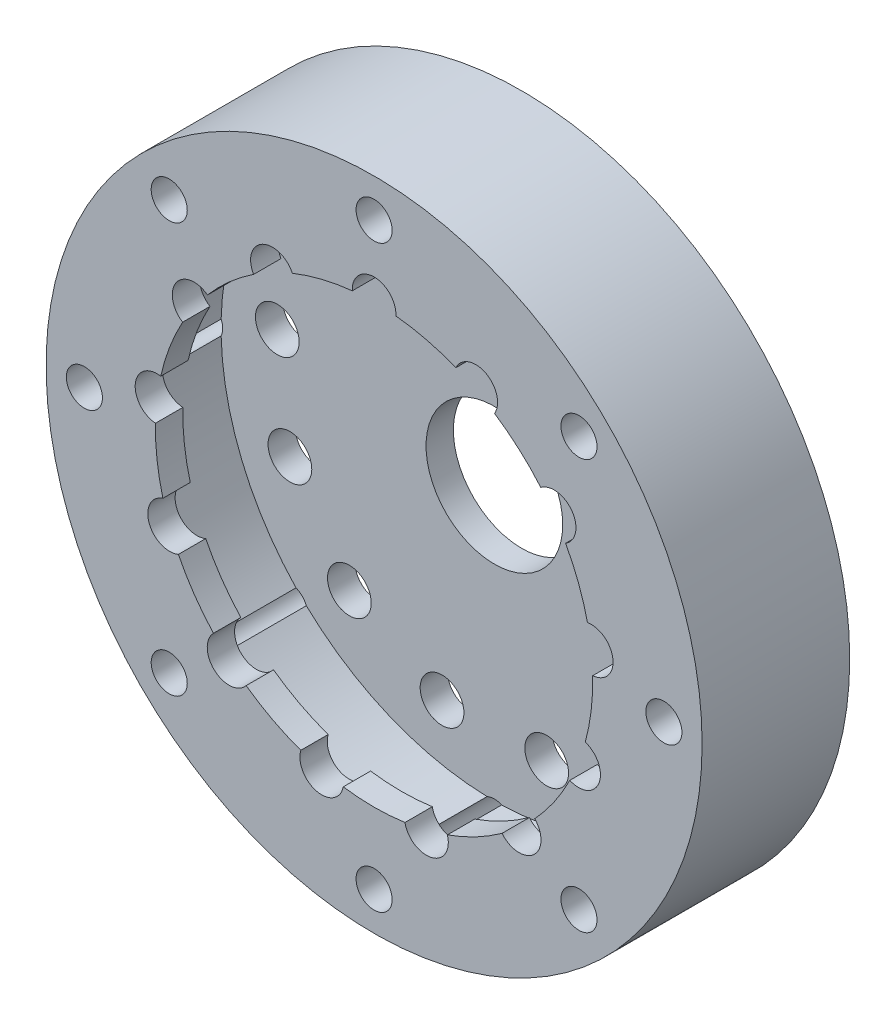
SolidWorks part; units mm, degrees
ref_plane "Front Plane" through (0, 0, 0) normal (0, 0, 1) x (1, 0, 0)
ref_plane "Top Plane" through (0, 0, 0) normal (0, 1, 0) x (1, 0, 0)
ref_plane "Right Plane" through (0, 0, 0) normal (1, 0, 0) x (0, 0, -1)
sketch "Sketch1" plane through (0, 0, 0) normal (0, 0, 1) x (1, 0, 0)
  circle A0 centre (0, 0) radius 60
  circle A1 centre (0, 0) radius 55 construction
  dimension "D1" = 120
  dimension "D2" = 5
extrude "Boss-Extrude1" add sketch "Sketch1" along normal blind 5
sketch "Sketch2" plane through (0, 0, 5) normal (0, 0, 1) x (1, 0, 0)
  circle A0 centre (0, 0) radius 60
  circle A1 centre (0, 0) radius 50
  circle A2 centre (0, 0) radius 60 construction
  dimension "D1" = 10
extrude "Boss-Extrude2" add sketch "Sketch2" along normal blind 22
sketch "Sketch3" plane through (0, 0, 27) normal (0, 0, 1) x (1, 0, 0)
  circle A0 centre (0, 0) radius 60
  circle A2 centre (0, 0) radius 60 construction
  circle A3 centre (0, 0) radius 40
  dimension "D1" = 80
extrude "Boss-Extrude3" add sketch "Sketch3" against normal blind 5
sketch "Sketch4" plane through (0, 0, 5) normal (0, 0, 1) x (1, 0, 0)
  circle A0 centre (0, 0) radius 12.5
  dimension "D1" = 25
extrude "Cut-Extrude1" cut sketch "Sketch4" against normal through all
sketch "Sketch5" plane through (0, 0, 27) normal (0, 0, 1) x (1, 0, 0)
  circle A14 centre (0, 40) radius 4
  circle A15 centre (0, 0) radius 40 construction
  circle A16 centre (18.5889, 35.4182) radius 4
  circle A17 centre (32.9194, 22.7226) radius 4
  circle A18 centre (39.7084, 4.8215) radius 4
  circle A19 centre (37.4006, -14.1842) radius 4
  circle A20 centre (26.5249, -29.9404) radius 4
  circle A21 centre (9.5726, -38.8377) radius 4
  circle A22 centre (-9.5726, -38.8377) radius 4
  circle A23 centre (-26.5249, -29.9404) radius 4
  circle A24 centre (-37.4006, -14.1842) radius 4
  circle A25 centre (-39.7084, 4.8215) radius 4
  circle A26 centre (-32.9194, 22.7226) radius 4
  circle A27 centre (-18.5889, 35.4182) radius 4
  point P30 (0, 0)
  dimension "D1" = 8
  dimension "D2" = 80
extrude "Cut-Extrude2" cut sketch "Sketch5" against normal through all
sketch "Sketch13" plane through (0, 0, 27) normal (0, 0, 1) x (1, 0, 0)
  circle A0 centre (0, 0) radius 53 construction
  circle A1 centre (0, 0) radius 60 construction
  point P5 (0, 53)
  point P6 (37.4767, 37.4767)
  point P9 (53, 0)
  point P10 (37.4767, -37.4767)
  point P11 (0, -53)
  point P12 (-37.4767, -37.4767)
  point P13 (-53, 0)
  point P14 (-37.4767, 37.4767)
  point P15 (0, 0)
  dimension "D1" = 7
  dimension "D2" = 8
sketch "Sketch16" plane through (0, 0, 27) normal (0, 0, 1) x (1, 0, 0)
  point P0 (0, 53)
  point P3 (37.4767, 37.4767)
  point P6 (53, 0)
  point P9 (37.4767, -37.4767)
  point P12 (0, -53)
  point P15 (-37.4767, -37.4767)
  point P18 (-53, 0)
  point P21 (-37.4767, 37.4767)
hole_wizard "M6 Clearance Hole1" positions "Sketch16" profile "Sketch15" hole size "M6" standard "ISO" end condition through all
sketch "Sketch15" plane through (0, 53, 27) normal (1, 0, 0) x (0, -1, 0)
  line L0 (0, 0) -> (0, 27)
  line L1 (0, 27) -> (3.3, 27)
  line L2 (3.3, 27) -> (3.3, 0)
  line L5 (3.3, 0) -> (0, 0)
  line L11 (0, -6.35) -> (0, 107.95) construction
  dimension "Thru Hole Dia." = 6.6
  dimension "Thru Hole Depth" = 27
